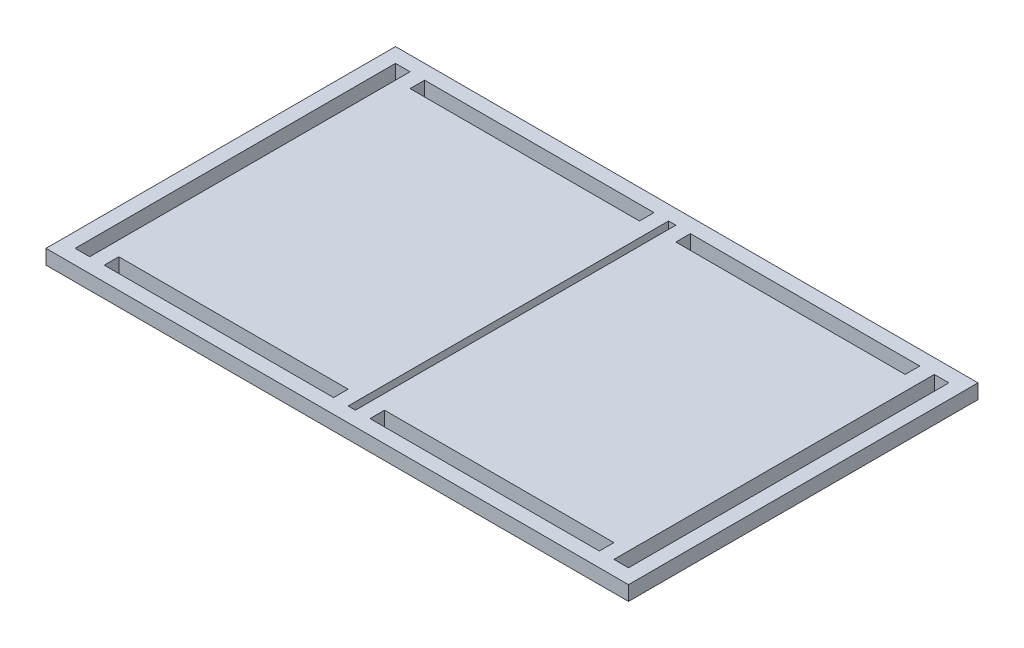
SolidWorks part; units mm, degrees
ref_plane "Front Plane" through (0, 0, 0) normal (0, 0, 1) x (1, 0, 0)
ref_plane "Top Plane" through (0, 0, 0) normal (0, 1, 0) x (1, 0, 0)
ref_plane "Right Plane" through (0, 0, 0) normal (1, 0, 0) x (0, 0, -1)
sketch "Sketch1" plane through (0, 0, 0) normal (0, 1, 0) x (1, 0, 0)
  line L0 (0, 76.2) -> (0, -76.2) construction
  line L1 (127, -76.2) -> (-127, -76.2)
  line L2 (127, -76.2) -> (127, 76.2)
  line L3 (127, 76.2) -> (-127, 76.2)
  line L4 (-127, -76.2) -> (-127, 76.2)
  line L5 (127, -76.2) -> (-127, 76.2) construction
  line L6 (127, 76.2) -> (-127, -76.2) construction
  line L11 (120.65, -69.85) -> (114.3, -69.85)
  line L12 (120.65, -69.85) -> (120.65, 69.85)
  line L13 (120.65, 69.85) -> (114.3, 69.85)
  line L14 (114.3, -69.85) -> (114.3, 69.85)
  line L15 (120.65, -69.85) -> (114.3, 69.85) construction
  line L16 (120.65, 69.85) -> (114.3, -69.85) construction
  line L17 (1.5875, -69.85) -> (-1.5875, -69.85)
  line L18 (1.5875, -69.85) -> (1.5875, 69.85)
  line L19 (1.5875, 69.85) -> (-1.5875, 69.85)
  line L20 (-1.5875, -69.85) -> (-1.5875, 69.85)
  line L21 (1.5875, -69.85) -> (-1.5875, 69.85) construction
  line L22 (1.5875, 69.85) -> (-1.5875, -69.85) construction
  line L23 (-120.65, -69.85) -> (-114.3, -69.85)
  line L24 (-114.3, -69.85) -> (-114.3, 69.85)
  line L25 (-120.65, -69.85) -> (-120.65, 69.85)
  line L26 (-120.65, 69.85) -> (-114.3, 69.85)
  line L27 (-127, 0) -> (127, 0) construction
  line L28 (-107.95, 69.85) -> (-7.9375, 69.85)
  line L29 (-107.95, 69.85) -> (-107.95, 63.5051)
  line L30 (-107.95, 63.5051) -> (-7.9375, 63.5051)
  line L31 (-7.9375, 69.85) -> (-7.9375, 63.5051)
  line L36 (7.9375, -63.5102) -> (107.95, -63.5102)
  line L37 (7.9375, -63.5102) -> (7.9375, -69.8551)
  line L38 (7.9375, -69.8551) -> (107.95, -69.8551)
  line L39 (107.95, -63.5102) -> (107.95, -69.8551)
  line L40 (7.9375, 63.5051) -> (107.95, 63.5051)
  line L41 (7.9375, 63.5051) -> (7.9375, 69.85)
  line L42 (7.9375, 69.85) -> (107.95, 69.85)
  line L43 (107.95, 63.5051) -> (107.95, 69.85)
  line L44 (-7.9375, -69.85) -> (-7.9375, -63.5051)
  line L45 (-107.95, -69.85) -> (-107.95, -63.5051)
  line L46 (-107.95, -69.85) -> (-7.9375, -69.85)
  line L47 (-107.95, -63.5051) -> (-7.9375, -63.5051)
  line L56 (-120.65, -57.15) -> (-114.3, -57.15)
  line L57 (-120.65, -44.45) -> (-114.3, -44.45)
  line L58 (-120.65, -31.75) -> (-114.3, -31.75)
  line L59 (-120.65, -19.05) -> (-114.3, -19.05)
  line L60 (-120.65, -6.35) -> (-114.3, -6.35)
  line L61 (-120.65, 6.35) -> (-114.3, 6.35)
  line L62 (-120.65, 19.05) -> (-114.3, 19.05)
  line L63 (-120.65, 31.75) -> (-114.3, 31.75)
  line L64 (-120.65, 44.45) -> (-114.3, 44.45)
  line L65 (-120.65, 57.15) -> (-114.3, 57.15)
  line L78 (120.65, -57.15) -> (114.3, -57.15)
  line L79 (120.65, -44.45) -> (114.3, -44.45)
  line L80 (120.65, -31.75) -> (114.3, -31.75)
  line L81 (120.65, -19.05) -> (114.3, -19.05)
  line L82 (120.65, -6.35) -> (114.3, -6.35)
  line L83 (120.65, 6.35) -> (114.3, 6.35)
  line L84 (120.65, 19.05) -> (114.3, 19.05)
  line L85 (120.65, 31.75) -> (114.3, 31.75)
  line L86 (120.65, 44.45) -> (114.3, 44.45)
  line L87 (120.65, 57.15) -> (114.3, 57.15)
  point P0 (0, 0)
  point P6 (117.475, 0)
  point P12 (0, 0)
  point P39 (107.95, -66.6826)
  point P86 (-117.475, 19.05)
  dimension "D1" = 254
  dimension "D2" = 152.4
  dimension "D3" = 6.35
  dimension "D4" = 6.35
  dimension "D5" = 6.35
  dimension "D6" = 6.35
  dimension "D7" = 6.35
  dimension "D8" = 3.175
  dimension "D9" = 6.35
  dimension "D10" = 6.35
  dimension "D11" = 6.3449
  dimension "D14" = 6.3449
  dimension "D15" = 6.35
  dimension "D16" = 6.35
  dimension "D17" = 6.35
  dimension "D18" = 6.35
  dimension "D19" = 6.3449
  dimension "D33" = 12.7
  dimension "D34" = 12.7
  dimension "D35" = 12.7
  dimension "D36" = 12.7
  dimension "D37" = 12.7
  dimension "D38" = 12.7
  dimension "D39" = 12.7
  dimension "D40" = 12.7
  dimension "D41" = 12.7
  dimension "D42" = 12.7
  dimension "D43" = 6.3449
  dimension "D44" = 6.35
  dimension "D45" = 6.35
extrude "Boss-Extrude1" add sketch "Sketch1" along normal blind 6.35 contours L4 L1 L2 L3 L43 L40 L41 L42 L11 L14 L13 L12 L17 L20 L19 L18 L25
